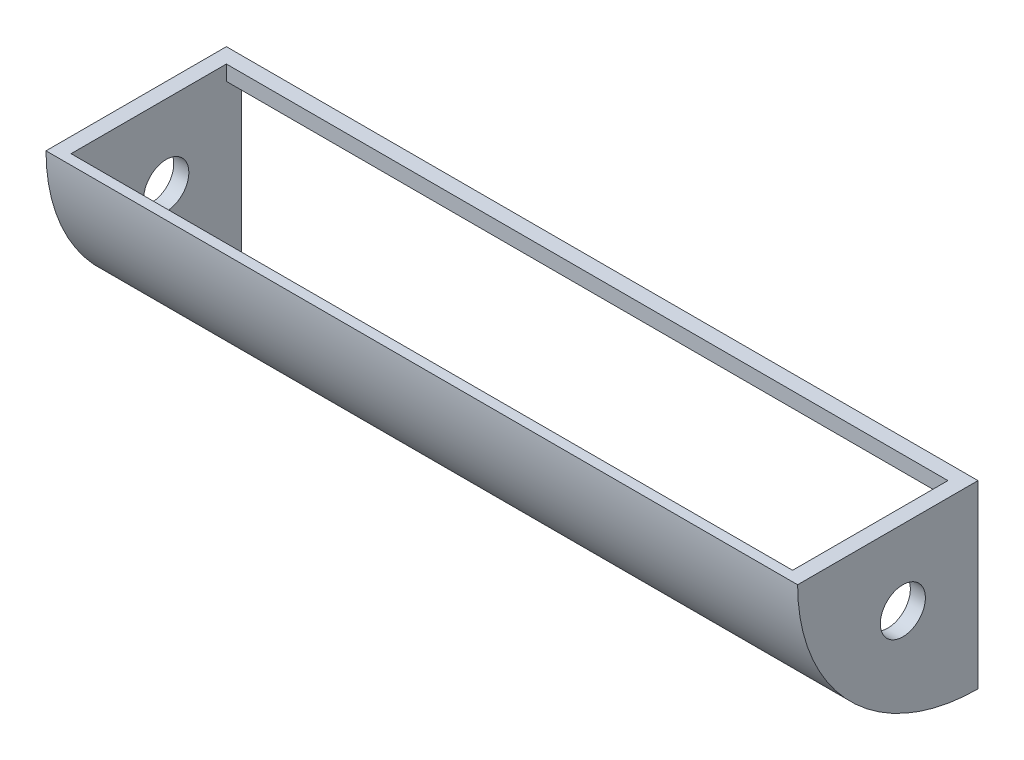
SolidWorks part; units mm, degrees
ref_plane "Front Plane" through (0, 0, 0) normal (0, 0, 1) x (1, 0, 0)
ref_plane "Top Plane" through (0, 0, 0) normal (0, 1, 0) x (1, 0, 0)
ref_plane "Right Plane" through (0, 0, 0) normal (1, 0, 0) x (0, 0, -1)
sketch "Sketch1" plane through (0, 0, 0) normal (1, 0, 0) x (0, 0, -1)
  line L0 (0, 0) -> (-304.8, 0)
  line L1 (0, 0) -> (0, -304.8)
  arc A0 (-304.8, 0) -> (0, -304.8) centre (0, 0) ccw
  dimension "D1" = 609.6
extrude "Boss-Extrude1" add sketch "Sketch1" along normal blind 25.4
sketch "Sketch2" plane through (25.4, 0, 0) normal (1, 0, 0) x (0, 0, -1)
  line L0 (-304.8, 0) -> (-287.8488, 0)
  line L1 (0, 0) -> (-304.8, 0) construction
  line L5 (-69.2283, -279.4) -> (-69.2283, -296.8341)
  line L7 (0, 0) -> (-25.4, 0)
  line L8 (0, 0) -> (0, -25.4)
  line L9 (0, -25.4) -> (-25.4, -25.4)
  line L10 (-25.4, 0) -> (-25.4, -25.4)
  arc A0 (-304.8, 0) -> (-69.2283, -296.8341) centre (0, 0) ccw
  arc A1 (-287.8488, 0) -> (-69.2283, -279.4) centre (0, 0) ccw
  dimension "D1" = 25.4
  dimension "D2" = 25.4
extrude "Boss-Extrude2" add sketch "Sketch2" along normal blind 609.6
ref_plane "Plane2" through (635, 0, 0) normal (1, 0, 0) x (0, 0, -1)
sketch "Sketch3" plane through (0, 0, 0) normal (-1, 0, 0) x (0, 0, 1)
  line L0 (0, 0) -> (304.8, 0) construction
  line L1 (0, -304.8) -> (0, 0) construction
  circle A0 centre (127, -127) radius 38.1
  dimension "D1" = 76.2
  dimension "D2" = 127
  dimension "D3" = 127
extrude "Cut-Extrude1" cut sketch "Sketch3" against normal blind 609.6
mirror "Mirror2" about plane through (635, 0, 0) normal (1, 0, 0) of "Boss-Extrude1", "Boss-Extrude2"
mirror "Mirror3" about plane through (635, 0, 0) normal (1, 0, 0) of "Boss-Extrude1"
mirror "Mirror4" about plane through (635, 0, 0) normal (1, 0, 0) of "Cut-Extrude1"
